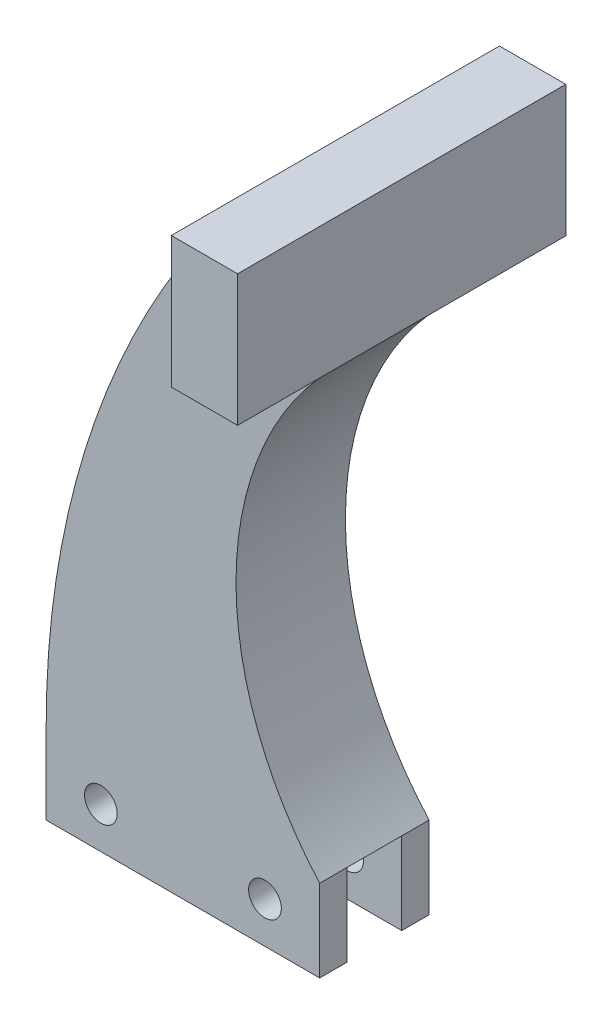
SolidWorks part; units mm, degrees
ref_plane "Front Plane" through (0, 0, 0) normal (0, 0, 1) x (1, 0, 0)
ref_plane "Top Plane" through (0, 0, 0) normal (0, 1, 0) x (1, 0, 0)
ref_plane "Right Plane" through (0, 0, 0) normal (1, 0, 0) x (0, 0, -1)
sketch "Sketch1" plane through (0, 0, 0) normal (0, 0, 1) x (1, 0, 0)
  line L0 (0, 35.15) -> (0, -10.65) construction
  line L1 (-15.875, 0) -> (15.875, 0)
  line L2 (-15.875, 0) -> (-15.875, 9.525)
  line L3 (19.05, 63.5) -> (19.05, 78.74)
  line L4 (15.875, 0) -> (15.875, 9.525)
  line L5 (19.05, 78.74) -> (11.3486, 78.74)
  arc A0 (19.05, 63.5) -> (15.875, 9.525) centre (44.2632, 34.936) ccw
  arc A1 (11.3486, 78.74) -> (-15.875, 9.525) centre (85.725, 9.525) ccw
  dimension "D5" = 203.2
  dimension "D6" = 38.1
  dimension "D1" = 31.75
  dimension "D2" = 9.525
  dimension "D3" = 63.5
  dimension "D4" = 19.05
  dimension "D7" = 15.24
extrude "Boss-Extrude1" add sketch "Sketch1" against normal blind 12.7
sketch "Sketch5" plane through (-15.875, 0, 0) normal (-1, 0, 0) x (0, 0, 1)
  line L0 (-6.35, 0) -> (-6.35, 10.0668) construction
  line L1 (-12.7, 0) -> (0, 0) construction
  line L2 (-9.525, 0) -> (-9.525, 9.525)
  line L4 (-9.525, 9.525) -> (-3.175, 9.525)
  line L5 (-3.175, 9.525) -> (-3.175, 0)
  line L6 (-3.175, 0) -> (-9.525, 0)
  dimension "D1" = 6.35
  dimension "D2" = 9.525
extrude "Cut-Extrude1" cut sketch "Sketch5" against normal through all
hole_wizard "#6 Clearance Hole1" positions "Sketch7" profile "Sketch6" hole size "#6" standard "ANSI Inch" end condition through all
sketch "Sketch7" plane through (0, 0, 0) normal (0, 0, 1) x (1, 0, 0)
  line L0 (0, 0) -> (0, 17.0045) construction
  line L3 (-15.875, 0) -> (15.875, 0) construction
  point P0 (9.525, 4.7625)
  point P2 (-9.525, 4.7625)
  dimension "D1" = 4.7625
  dimension "D2" = 19.05
sketch "Sketch6" plane through (9.525, 4.7625, 0) normal (1, 0, 0) x (0, -1, 0)
  line L0 (0, 0) -> (0, 12.7)
  line L1 (0, 12.7) -> (1.8986, 12.7)
  line L2 (1.8986, 12.7) -> (1.8986, 0)
  line L5 (1.8986, 0) -> (0, 0)
  line L11 (0, -6.35) -> (0, 107.95) construction
  dimension "Thru Hole Dia." = 3.7973
  dimension "Thru Hole Depth" = 12.7
ref_plane "Plane1" through (0, 0, -6.35) normal (0, 0, 1) x (1, 0, 0)
sketch "Sketch9" plane through (0, 0, -6.35) normal (0, 0, 1) x (1, 0, 0)
  line L0 (19.05, 78.74) -> (11.3486, 78.74)
  line L1 (11.3486, 78.74) -> (11.3486, 63.5)
  line L2 (11.3486, 63.5) -> (19.05, 63.5)
  line L3 (19.05, 63.5) -> (19.05, 78.74)
extrude "Boss-Extrude2" add sketch "Sketch9" along normal mid plane 38.1
